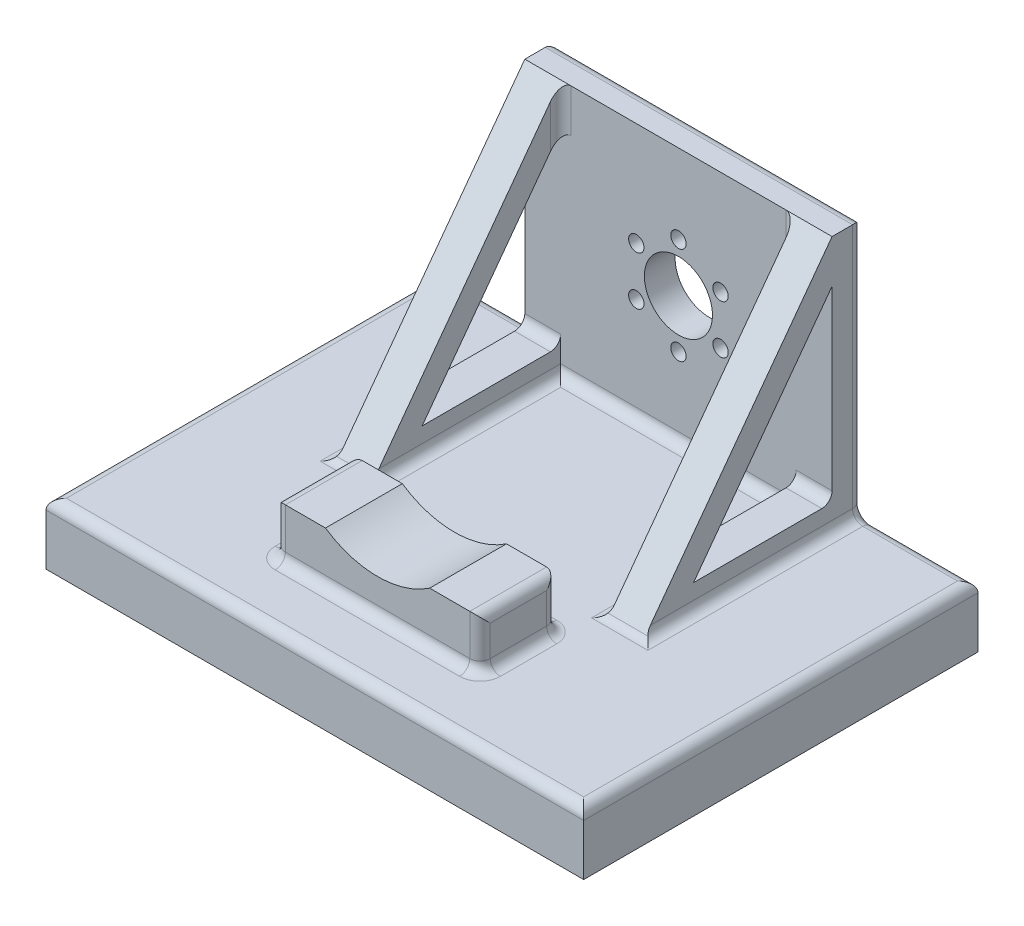
SolidWorks part; units mm, degrees
ref_plane "Front Plane" through (0, 0, 0) normal (0, 0, 1) x (1, 0, 0)
ref_plane "Top Plane" through (0, 0, 0) normal (0, 1, 0) x (1, 0, 0)
ref_plane "Right Plane" through (0, 0, 0) normal (1, 0, 0) x (0, 0, -1)
sketch "Sketch1" plane through (0, 0, 0) normal (1, 0, 0) x (0, 0, -1)
  line L0 (0, 0) -> (0, 50)
  line L1 (0, 50) -> (6, 50)
  line L2 (6, 50) -> (6, -12)
  line L3 (6, -12) -> (-71, -12)
  line L4 (-71, -12) -> (-71, 0)
  line L5 (-71, 0) -> (0, 0)
  dimension "D1" = 6
  dimension "D2" = 50
  dimension "D3" = 71
  dimension "D4" = 12
extrude "Boss-Extrude1" add sketch "Sketch1" along normal mid plane 105
sketch "Sketch6" plane through (0, 0, 0) normal (0, 1, 0) x (1, 0, 0)
  line L3 (0, -51.25) -> (0, -71) construction
  line L4 (52.5, -71) -> (-52.5, -71) construction
  line L6 (20, -43.75) -> (-20, -43.75)
  line L7 (20, -43.75) -> (20, -58.75)
  line L8 (20, -58.75) -> (-20, -58.75)
  line L9 (-20, -43.75) -> (-20, -58.75)
  line L10 (20, -43.75) -> (-20, -58.75) construction
  line L11 (20, -58.75) -> (-20, -43.75) construction
  dimension "D1" = 40
  dimension "D2" = 15
  dimension "D3" = 12.25
extrude "Boss-Extrude3" add sketch "Sketch6" along normal blind 10
sketch "Sketch9" plane through (0, 0, -6) normal (0, 0, -1) x (-1, 0, 0)
  line L0 (-52.5, 50) -> (52.5, 50) construction
  line L6 (52.5, 50) -> (52.5, 0) construction
  circle A2 centre (0, 25) radius 6.65
  circle A3 centre (0, 34.5) radius 1.5
  point P6 (0, 50)
  point P12 (52.5, 25)
  dimension "D1" = 13.3
  dimension "D2" = 3
  dimension "D3" = 9.5
extrude "Cut-Extrude4" cut sketch "Sketch9" against normal through all
pattern_circular "CirPattern2" count 6 over 360 about axis through (0, 25, 0) along (0, 0, 1) of "Cut-Extrude4"
sketch "Sketch10" plane through (0, 0, 0) normal (0, 0, 1) x (1, 0, 0)
  circle A0 centre (0, 25) radius 18.125
  circle A1 centre (0, 25) radius 6.65 construction
  dimension "D1" = 36.25
extrude "Cut-Extrude5" cut sketch "Sketch10" along normal through all
fillet "Fillet3" radius 2 10 edges at (0, 0, 43.75) (0, 0, 58.75) (20, 5, 58.75) (20, 10, 51.25) (20, 5, 43.75) (20, 0, 51.25) (-20, 5, 43.75) (-20, 10, 51.25) (-20, 5, 58.75) (-20, 0, 51.25)
sketch "Sketch11" plane through (0, 0, 0) normal (0, 0, 1) x (1, 0, 0)
  line L0 (52.5, 0) -> (-52.5, 0) construction
  line L1 (-52.5, 50) -> (-30, 50)
  line L2 (-52.5, 50) -> (-52.5, 0)
  line L3 (-52.5, 0) -> (-30, 0)
  line L4 (-30, 50) -> (-30, 0)
  line L5 (-30, 50) -> (30, 50) construction
  line L6 (52.5, 50) -> (-52.5, 50) construction
  point P11 (0, 50)
  point P12 (0, 50)
  dimension "D1" = 60
extrude "Cut-Extrude6" cut sketch "Sketch11" against normal through all
mirror "Mirror1" about plane through (0, 0, 0) normal (1, 0, 0) of "Cut-Extrude6"
sketch "Sketch12" plane through (0, 0, 0) normal (0, 0, 1) x (1, 0, 0)
  circle A0 centre (0, 25) radius 18 construction
  dimension "D1" = 36
sketch "Sketch13" plane through (30, 0, 0) normal (1, 0, 0) x (0, 0, -1)
  line L0 (0, 0) -> (-36.9622, 0)
  line L1 (-36.9622, 0) -> (0, 50)
  line L2 (0, 0) -> (0, 50) construction
  line L3 (0, 50) -> (0, 0)
  point P7 (0, 50)
  point P9 (-36.9622, 0)
extrude "Boss-Extrude4" add sketch "Sketch13" against normal blind 7
sketch "Sketch14" plane through (30, 0, 0) normal (1, 0, 0) x (0, 0, -1)
  line L10 (0, 0) -> (0, 50) construction
  line L11 (0, 0) -> (0, 50) construction
  line L12 (-27.0481, 5) -> (0, 5)
  line L13 (0, 5) -> (0, 41.5889)
  line L14 (1, 42.9416) -> (-27.0481, 5)
  line L15 (-27.0481, 5) -> (1, 5)
  line L16 (1, 5) -> (1, 42.9416)
  line L17 (0, 41.5889) -> (-27.0481, 5)
  dimension "D1" = 5
extrude "Cut-Extrude8" cut sketch "Sketch14" against normal through all contours L17 L12 L13
mirror "Mirror2" about plane through (0, 0, 0) normal (1, 0, 0) of "Boss-Extrude4", "Cut-Extrude8"
sketch "Sketch15" plane through (0, 0, -6) normal (0, 0, -1) x (-1, 0, 0)
  line L0 (52.5, -12) -> (52.5, 0) construction
  line L1 (52.5, 0) -> (30, 0) construction
  line L2 (-52.5, -12) -> (52.5, -12) construction
  line L3 (-52.5, -12) -> (-52.5, 0) construction
  line L4 (-52.5, 0) -> (-30, 0) construction
  line L5 (52.5, -12) -> (52.5, 0)
  line L6 (52.5, 0) -> (30, 0)
  line L7 (-52.5, -12) -> (52.5, -12)
  line L8 (-52.5, -12) -> (-52.5, 0)
  line L9 (-52.5, 0) -> (-30, 0)
  line L10 (-30, 0) -> (30, 0)
fillet "Fillet5" radius 2 19 edges at (30, 25, -6) (-30, 25, -6) (23, 0, 18.4811) (26.5, 0, 36.9622) (30, 0, 15.4811) (41.25, 0, -6) (52.5, 0, 32.5) (0, 0, 71) (-52.5, 0, 32.5) (-41.25, 0, -6) (-30, 0, 15.4811) (-26.5, 0, 36.9622) (-23, 0, 18.4811) (0, 0, 0) (0, 50, -6) (23, 45.7944, 0) (-23, 45.7944, 0) (26.5, 5, 0) (-26.5, 5, 0)
equation "\"face_w\"= 60"
equation "\"face_t\"= 7mm"
